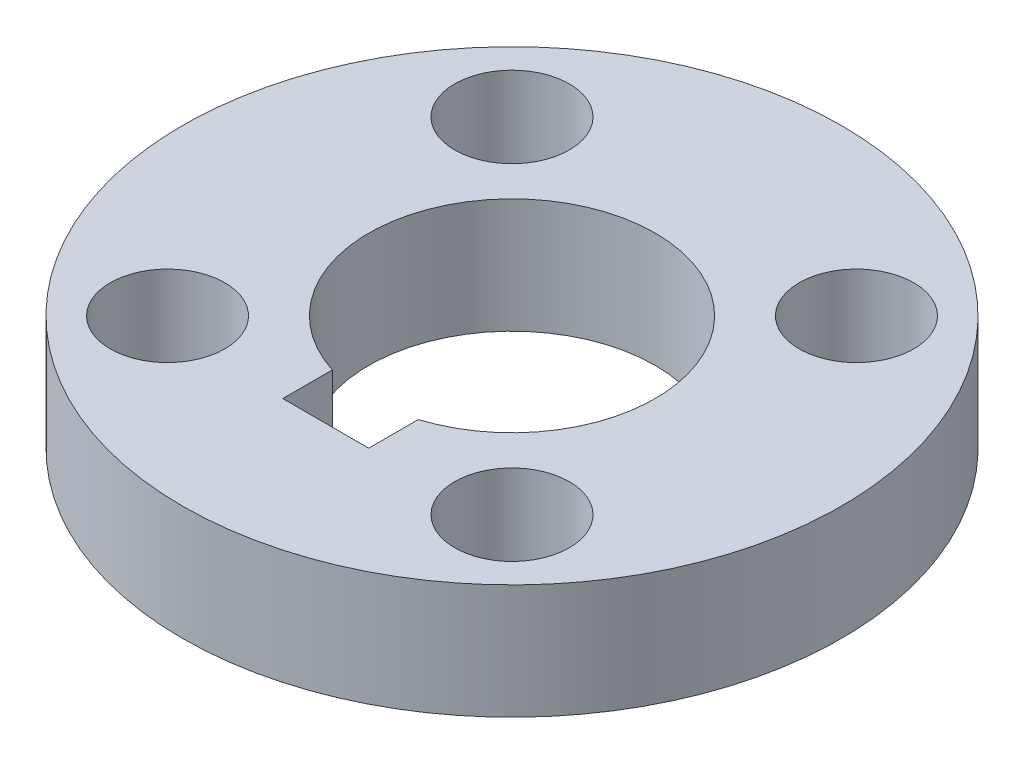
SolidWorks part; units mm, degrees
material "Acier non allié"
ref_plane "Plan de face" through (0, 0, 0) normal (0, 0, 1) x (1, 0, 0)
ref_plane "Plan de dessus" through (0, 0, 0) normal (0, 1, 0) x (1, 0, 0)
ref_plane "Plan de droite" through (0, 0, 0) normal (1, 0, 0) x (0, 0, -1)
sketch "Esquisse1" plane through (0, 0, 0) normal (0, 1, 0) x (1, 0, 0)
  circle A0 centre (0, 0) radius 10
  circle A1 centre (0, 0) radius 23
extrude "Boss.-Extru.1" add sketch "Esquisse1" along normal blind 8
sketch3d "Esquisse3D1" plane through (0, 0, 0) normal (0, 0, 1) x (1, 0, 0)
  dimension "D1" = 10
sketch "Esquisse2" plane through (0, 0, 10) normal (0, 0, 1) x (1, 0, 0)
  line L1 (0, 0) -> (0, 12) construction
  line L2 (-3, 0) -> (-3, 12)
  line L3 (3, 0) -> (3, 12)
  arc A0 (-3, 0) -> (3, 0) centre (0, 0) ccw
  arc A1 (3, 12) -> (-3, 12) centre (0, 12) ccw
  point P3 (0, 6)
extrude "Enlèv. mat.-Extru.1" cut sketch "Esquisse2" against normal blind 1 and the other way blind 3
sketch "Esquisse4" plane through (0, 0, 0) normal (0, -1, 0) x (1, 0, 0)
  line L0 (0, 0) -> (12.0208, 12.0208) construction
  line L1 (97.889, 0) -> (-97.889, 0) construction
  circle A0 centre (12.0208, 12.0208) radius 4
  dimension "D1" = 8
  dimension "D2" = 17
  dimension "D3" = 45
extrude "Enlèv. mat.-Extru.2" cut sketch "Esquisse4" against normal through all
pattern_circular "Répétition circulaire1" count 4 over 360 about axis through (0, 0, 0) along (0, 1, 0) of "Enlèv. mat.-Extru.2"
